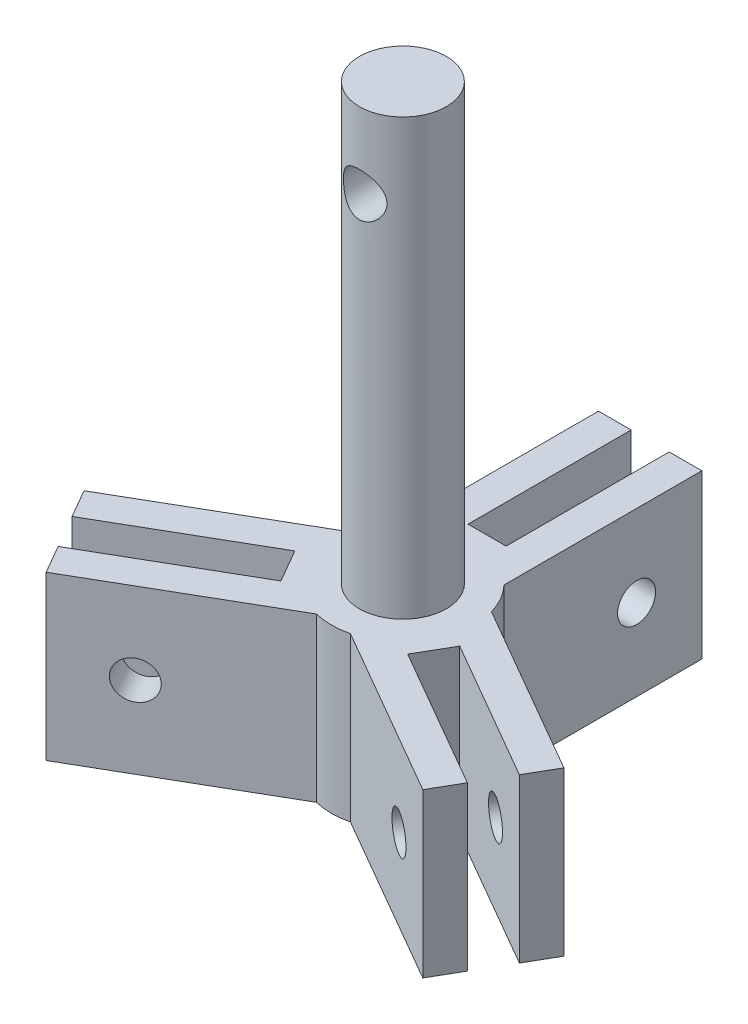
SolidWorks part; units mm, degrees
ref_plane "前基準面" through (0, 0, 0) normal (0, 0, 1) x (1, 0, 0)
ref_plane "上基準面" through (0, 0, 0) normal (0, 1, 0) x (1, 0, 0)
ref_plane "右基準面" through (0, 0, 0) normal (1, 0, 0) x (0, 0, -1)
sketch "草圖1" plane through (0, 0, 0) normal (0, 1, 0) x (1, 0, 0)
  line L0 (6.315, 1.8389) -> (22.0705, -7.2576)
  line L2 (-4.75, 4.5495) -> (-4.75, 22.7424)
  line L3 (-4.75, 22.7424) -> (-1.75, 22.7424)
  line L4 (4.75, 4.5495) -> (4.75, 22.7424)
  line L5 (22.0705, -7.2576) -> (20.5705, -9.8557)
  line L7 (-1.75, 22.7424) -> (-1.75, 7.7424)
  line L8 (-1.75, 7.7424) -> (1.75, 7.7424)
  line L9 (1.75, 22.7424) -> (1.75, 7.7424)
  line L10 (1.75, 22.7424) -> (4.75, 22.7424)
  line L11 (20.5705, -9.8557) -> (7.5801, -2.3557)
  line L12 (7.5801, -2.3557) -> (5.8301, -5.3868)
  line L13 (18.8205, -12.8868) -> (5.8301, -5.3868)
  line L14 (18.8205, -12.8868) -> (17.3205, -15.4848)
  line L15 (1.565, -6.3884) -> (17.3205, -15.4848)
  line L17 (-1.565, -6.3884) -> (-17.3205, -15.4848)
  line L18 (-17.3205, -15.4848) -> (-18.8205, -12.8868)
  line L19 (-18.8205, -12.8868) -> (-5.8301, -5.3868)
  line L20 (-5.8301, -5.3868) -> (-7.5801, -2.3557)
  line L21 (-20.5705, -9.8557) -> (-7.5801, -2.3557)
  line L22 (-20.5705, -9.8557) -> (-22.0705, -7.2576)
  line L23 (-6.315, 1.8389) -> (-22.0705, -7.2576)
  arc A1 (-1.565, -6.3884) -> (1.565, -6.3884) centre (0, 0) ccw
  arc A2 (6.315, 1.8389) -> (4.75, 4.5495) centre (0, 0) ccw
  arc A3 (-4.75, 4.5495) -> (-6.315, 1.8389) centre (0, 0) ccw
  point P29 (0, 0)
  dimension "D9" = 13.1545
  dimension "D1" = 18.1929
  dimension "D2" = 9.5
  dimension "D3" = 3.5
  dimension "D4" = 15
  dimension "D5" = 3
  dimension "D7" = 18.1929
  dimension "D6" = 3
extrude "填料-伸長1" add sketch "草圖1" along normal blind 15 contours L0 L5 L11 L12 L13 L14 L15 A1 L17 L18 L19 L20 L21 L22 L23 A3 L2 L3 L7 L8 L9 L10 L4 A2
sketch "草圖2" plane through (0, 15, 0) normal (0, 1, 0) x (1, 0, 0)
  circle A0 centre (0, 0) radius 4
  dimension "D1" = 8
extrude "填料-伸長2" add sketch "草圖2" along normal blind 40
sketch "草圖3" plane through (4.75, 0, 0) normal (1, 0, 0) x (0, 0, -1)
  line L0 (22.7424, 15) -> (22.7424, 0) construction
  circle A0 centre (16.7424, 7.5) radius 1.75
  point P4 (0, 0)
  point P5 (22.7424, 7.5)
  dimension "D1" = 3.5
  dimension "D2" = 6
extrude "除料-伸長1" cut sketch "草圖3" against normal blind 15
sketch "草圖4" plane through (-2.375, 0, -4.1136) normal (-0.5, 0, -0.866) x (-0.866, 0, 0.5)
  line L0 (22.7424, 15) -> (22.7424, 0) construction
  circle A0 centre (16.7424, 7.5) radius 1.75
  point P4 (0, 0)
  point P5 (22.7424, 7.5)
  dimension "D1" = 3.5
  dimension "D2" = 6
extrude "除料-伸長2" cut sketch "草圖4" against normal blind 15
sketch "草圖5" plane through (-2.375, 0, 4.1136) normal (-0.5, 0, 0.866) x (0.866, 0, 0.5)
  line L0 (22.7424, 15) -> (22.7424, 0) construction
  circle A0 centre (16.7424, 7.5) radius 1.75
  point P4 (0, 0)
  point P5 (22.7424, 7.5)
  dimension "D1" = 3.5
  dimension "D2" = 6
extrude "除料-伸長3" cut sketch "草圖5" against normal blind 15
ref_plane "平面1" through (0, 0, 4) normal (0, 0, 1) x (1, 0, 0)
sketch "草圖7" plane through (0, 0, 4) normal (0, 0, 1) x (1, 0, 0)
  line L1 (0, 41.1753) -> (0, 55) construction
  circle A0 centre (0, 48) radius 2
  spline S0 degree 1 poles (0, 155) (0, 55) knots 0 0 1 1 construction
  point P3 (0, 0)
  dimension "D1" = 4
  dimension "D2" = 7
extrude "除料-伸長4" cut sketch "草圖7" against normal blind 15
